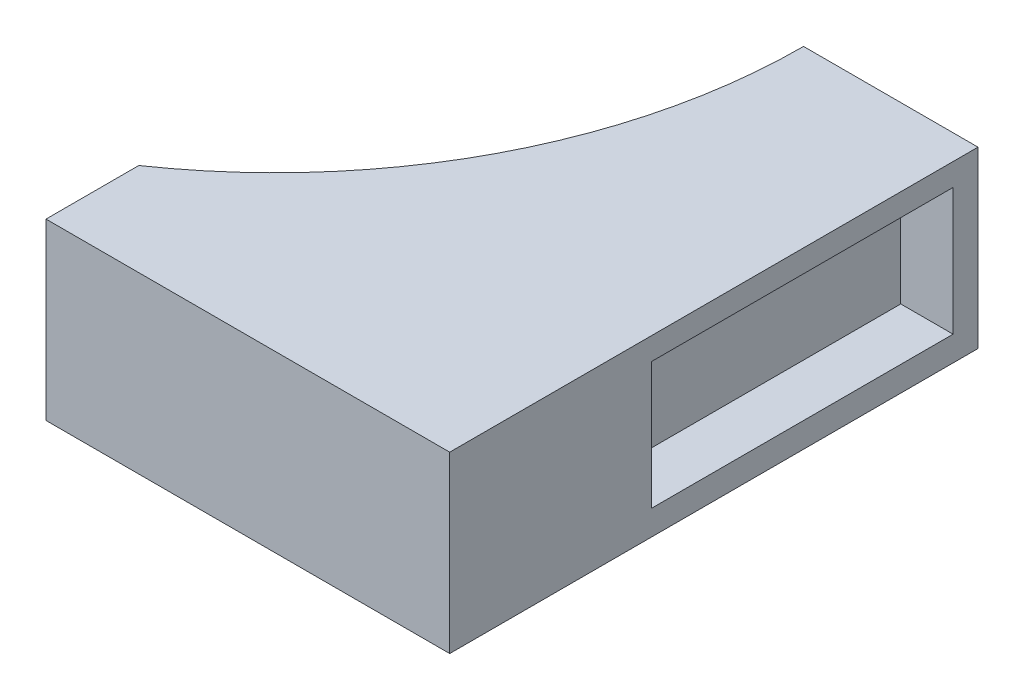
SolidWorks part; units mm, degrees
ref_plane "Front Plane" through (0, 0, 0) normal (0, 0, 1) x (1, 0, 0)
ref_plane "Top Plane" through (0, 0, 0) normal (0, 1, 0) x (1, 0, 0)
ref_plane "Right Plane" through (0, 0, 0) normal (1, 0, 0) x (0, 0, -1)
other "Configuration Table"
sketch "Sketch1" plane through (0, 0, 0) normal (0, 1, 0) x (1, 0, 0)
  line L1 (7, 21.2) -> (-21.2, 21.2)
  line L2 (0, 0) -> (7, 0)
  line L3 (7, 0) -> (7, 21.2)
  arc A0 (-21.2, 21.2) -> (0, 0) centre (-21.2, 0) cw
  dimension "D1" = 21.2
  dimension "D2" = 7
  dimension "D3" = 21.2
extrude "Boss-Extrude1" add sketch "Sketch1" along normal blind 7
sketch "Sketch2" plane through (0, 7, 0) normal (0, 1, 0) x (1, 0, 0)
  line L0 (-9.2, 17.4768) -> (-9.2, 21.2)
  line L1 (7, 21.2) -> (-21.2, 21.2) construction
  line L2 (-9.2, 21.2) -> (-21.2, 21.2)
  arc A0 (0, 0) -> (-21.2, 21.2) centre (-21.2, 0) ccw construction
  arc A1 (-21.2, 21.2) -> (-9.2, 17.4768) centre (-21.2, 0) cw
  dimension "D1" = 12
extrude "Cut-Extrude1" cut sketch "Sketch2" against normal through all
sketch "Sketch5" plane through (0, 0, 0) normal (1, 0, 0) x (0, 0, -1)
  line L1 (17, 6) -> (2, 6)
  line L2 (17, 6) -> (17, 3)
  line L3 (17, 3) -> (2, 3)
  line L4 (2, 6) -> (2, 3)
  line L5 (17.4768, 7) -> (0, 7) construction
  line L6 (0, 7) -> (0, 0) construction
  dimension "D1" = 15
  dimension "D2" = 3
  dimension "D3" = 1
  dimension "D4" = 2
extrude "Cut-Extrude3" cut sketch "Sketch5" against normal blind 10
sketch "Sketch6" plane through (7, 0, 0) normal (1, 0, 0) x (0, 0, -1)
  line L0 (0, 7) -> (0, 0) construction
  line L1 (1, 1) -> (13.1, 1)
  line L2 (1, 1) -> (1, 6.1)
  line L3 (1, 6.1) -> (13.1, 6.1)
  line L4 (13.1, 1) -> (13.1, 6.1)
  line L5 (0, 0) -> (21.2, 0) construction
  dimension "D1" = 1
  dimension "D2" = 12.1
  dimension "D3" = 5.1
  dimension "D4" = 1
extrude "Cut-Extrude4" cut sketch "Sketch6" against normal blind 2.1
mirror "Mirror1" about plane through (0, 7, 0) normal (0, 0, -1) of bodies 107
delete or keep bodies "Body-Delete/Keep 1" type keep bodies bodies 108
